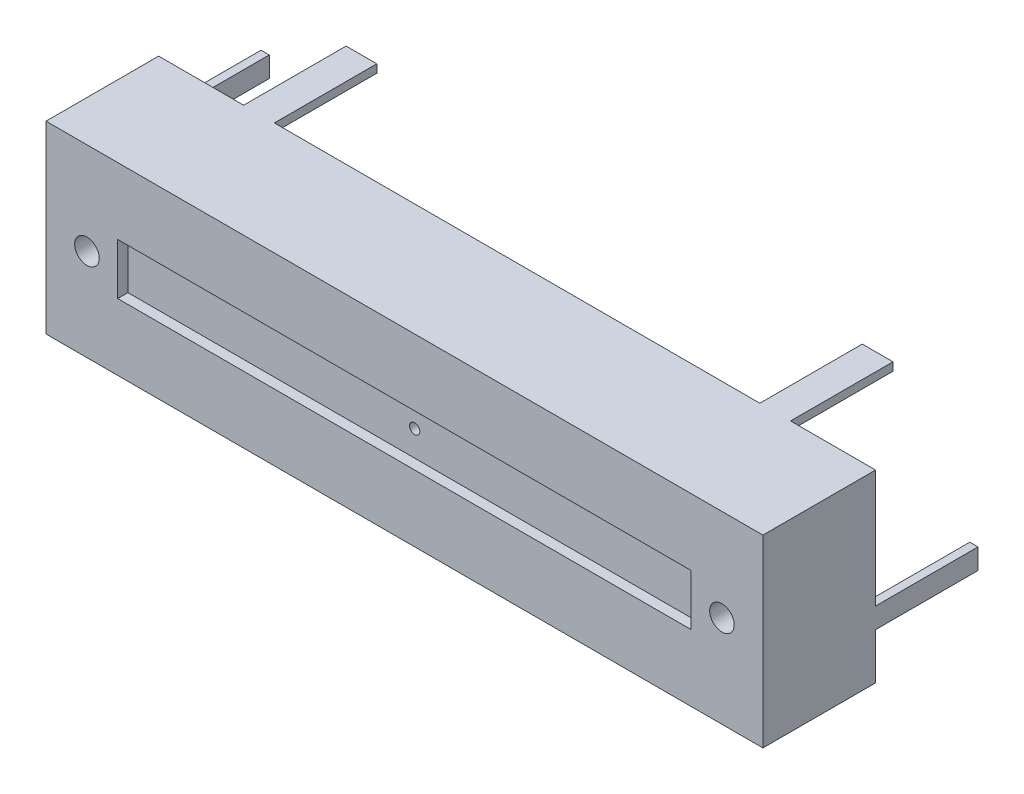
SolidWorks part; units mm, degrees
material "Melaminharz"
ref_plane "Ebene vorne" through (0, 0, 0) normal (0, 0, 1) x (1, 0, 0)
ref_plane "Ebene oben" through (0, 0, 0) normal (0, 1, 0) x (1, 0, 0)
ref_plane "Ebene rechts" through (0, 0, 0) normal (1, 0, 0) x (0, 0, -1)
sketch "body" plane through (0, 0, 0) normal (0, 0, 1) x (1, 0, 0)
  line L1 (-17.5, 4.5) -> (17.5, 4.5)
  line L2 (-17.5, 4.5) -> (-17.5, -4.5)
  line L3 (-17.5, -4.5) -> (17.5, -4.5)
  line L4 (17.5, 4.5) -> (17.5, -4.5)
  line L5 (-17.5, 4.5) -> (17.5, -4.5) construction
  line L6 (-17.5, -4.5) -> (17.5, 4.5) construction
  point P0 (0, 0)
  dimension "D1" = 35
  dimension "D2" = 9
extrude "-body" add sketch "body" along normal blind 5.5
sketch "holes" plane through (0, 0, 5.5) normal (0, 0, 1) x (1, 0, 0)
  line L0 (-17.5, 0) -> (17.5, 0) construction
  line L1 (-17.5, 4.5) -> (-17.5, -4.5) construction
  line L2 (17.5, -4.5) -> (17.5, 4.5) construction
  circle A0 centre (-15.5, 0) radius 0.6
  circle A1 centre (15.5, 0) radius 0.6
  dimension "D1" = 1.2
  dimension "D2" = 31
  dimension "D3" = 2
extrude "-holes" cut sketch "holes" against normal blind 1
sketch "channel" plane through (0, 0, 5.5) normal (0, 0, 1) x (1, 0, 0)
  line L1 (-14, 1.25) -> (14, 1.25)
  line L2 (-14, 1.25) -> (-14, -1.25)
  line L3 (-14, -1.25) -> (14, -1.25)
  line L4 (14, 1.25) -> (14, -1.25)
  line L5 (-14, 1.25) -> (14, -1.25) construction
  line L6 (-14, -1.25) -> (14, 1.25) construction
  point P0 (0, 0)
  dimension "D1" = 28
  dimension "D2" = 2.5
extrude "-channel" cut sketch "channel" against normal blind 0.5
sketch "connection pins" plane through (0, 0, 0) normal (0, 0, -1) x (-1, 0, 0)
  line L0 (-17.5, 4.5) -> (17.5, 4.5) construction
  line L1 (-13.35, 4.5) -> (-11.85, 4.5)
  line L2 (-13.35, 4.5) -> (-13.35, 4.1)
  line L3 (-13.35, 4.1) -> (-11.85, 4.1)
  line L4 (-11.85, 4.5) -> (-11.85, 4.1)
  line L5 (17.5, -4.5) -> (-17.5, -4.5) construction
  line L6 (11.85, 4.5) -> (13.35, 4.5)
  line L7 (11.85, 4.5) -> (11.85, 4.1)
  line L8 (11.85, 4.1) -> (13.35, 4.1)
  line L9 (13.35, 4.5) -> (13.35, 4.1)
  line L10 (-12.15, -4.5) -> (-10.65, -4.5)
  line L11 (-12.15, -4.5) -> (-12.15, -4.1)
  line L12 (-12.15, -4.1) -> (-10.65, -4.1)
  line L13 (-10.65, -4.5) -> (-10.65, -4.1)
  line L14 (-17.5, -4.5) -> (-17.5, 4.5) construction
  line L15 (-17.5, -1.25) -> (-17.1, -1.25)
  line L16 (-17.5, -1.25) -> (-17.5, -2.25)
  line L17 (-17.5, -2.25) -> (-17.1, -2.25)
  line L18 (-17.1, -1.25) -> (-17.1, -2.25)
  line L19 (17.5, 4.5) -> (17.5, -4.5) construction
  line L20 (10.65, -4.5) -> (12.15, -4.5)
  line L21 (10.65, -4.5) -> (10.65, -4.1)
  line L22 (10.65, -4.1) -> (12.15, -4.1)
  line L23 (12.15, -4.5) -> (12.15, -4.1)
  line L24 (17.5, 2.25) -> (17.1, 2.25)
  line L25 (17.5, 2.25) -> (17.5, 1.25)
  line L26 (17.5, 1.25) -> (17.1, 1.25)
  line L27 (17.1, 2.25) -> (17.1, 1.25)
  line L28 (-17.1, -1.25) -> (20.1267, -1.25) construction
  line L29 (17.1, 2.25) -> (-17.5, 2.25) construction
  line L31 (17.5, -1.25) -> (17.1, -1.25)
  line L32 (17.5, -1.25) -> (17.5, -2.25)
  line L33 (17.5, -2.25) -> (17.1, -2.25)
  line L34 (17.1, -1.25) -> (17.1, -2.25)
  dimension "D1" = 0.4
  dimension "D2" = 0.4
  dimension "D3" = 0.4
  dimension "D4" = 0.4
  dimension "D5" = 0.4
  dimension "D6" = 0.4
  dimension "D7" = 1.5
  dimension "D8" = 1.5
  dimension "D9" = 1.5
  dimension "D10" = 1.5
  dimension "D11" = 25.2
  dimension "D12" = 22.8
  dimension "D13" = 1
  dimension "D14" = 1
  dimension "D15" = 5.35
  dimension "D16" = 4.15
  dimension "D17" = 3.5
  dimension "D18" = 2.25
  dimension "D19" = 2.25
extrude "-connection pins" add sketch "connection pins" along normal blind 5
sketch "Skizze1" plane through (0, 0, 5) normal (0, 0, 1) x (1, 0, 0)
  line L0 (15.5, 0) -> (-15.5, 0) construction
  circle A0 centre (0, 0) radius 0.25
  dimension "D1" = 0.5
extrude "Schnitt-Linear austragen1" cut sketch "Skizze1" against normal through all
